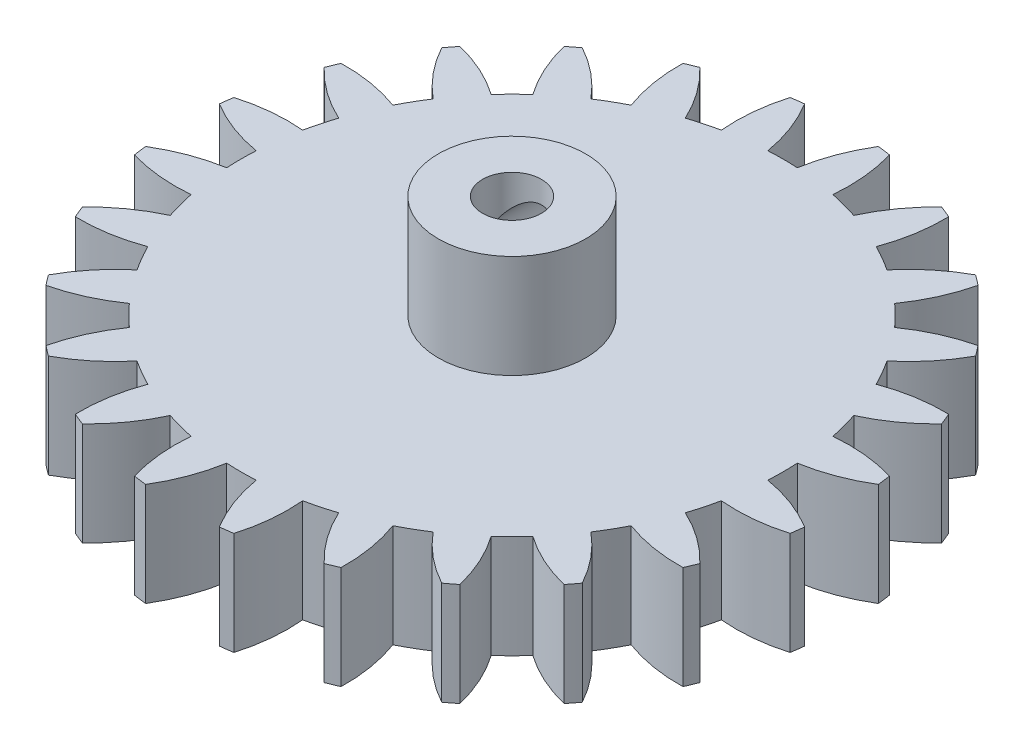
SolidWorks part; units mm, degrees
ref_plane "Front Plane" through (0, 0, 0) normal (0, 0, 1) x (1, 0, 0)
ref_plane "Top Plane" through (0, 0, 0) normal (0, 1, 0) x (1, 0, 0)
ref_plane "Right Plane" through (0, 0, 0) normal (1, 0, 0) x (0, 0, -1)
sketch "Sketch1" plane through (0, 0, 0) normal (0, 1, 0) x (1, 0, 0)
  circle A0 centre (0, 0) radius 22.5
  dimension "D1" = 45
extrude "Boss-Extrude1" add sketch "Sketch1" along normal blind 7
sketch "Sketch2" plane through (0, 7, 0) normal (0, 1, 0) x (1, 0, 0)
  line L0 (-1, 18.3607) -> (1, 18.3607) construction
  line L1 (-12.235, 16.4288) -> (12.235, 16.4288) construction
  line L2 (0, 22.3607) -> (0, 0) construction
  line L4 (2.5, 22.3607) -> (-2.5, 22.3607) construction
  arc A0 (2.5, 22.3607) -> (1, 18.3607) centre (12.235, 16.4288) ccw
  circle A1 centre (0, 0) radius 22.5 construction
  arc A2 (-2.5, 22.3607) -> (-1, 18.3607) centre (-12.235, 16.4288) cw
  arc A3 (1, 18.3607) -> (-1, 18.3607) centre (0, 0) ccw
  arc A4 (2.5, 22.3607) -> (-2.5, 22.3607) centre (0, 0) ccw
  point P8 (0, 16.4288)
  dimension "D1" = 2
  dimension "D2" = 5
  dimension "D3" = 4
  dimension "D4" = 24.47
extrude "Cut-Extrude1" cut sketch "Sketch2" against normal through all
pattern_circular "CirPattern1" count 24 every 15 about axis through (0, 0, 0) along (0, 1, 0) of "Cut-Extrude1"
sketch "Sketch3" plane through (0, 7, 0) normal (0, 1, 0) x (1, 0, 0)
  circle A0 centre (0, 0) radius 5
  dimension "D1" = 10
extrude "Boss-Extrude2" add sketch "Sketch3" along normal blind 7
sketch "Sketch4" plane through (0, 14, 0) normal (0, 1, 0) x (1, 0, 0)
  circle A0 centre (0, 0) radius 2
extrude "Cut-Extrude2" cut sketch "Sketch4" against normal through all
sketch "Sketch5" plane through (0, 0, 0) normal (0, 0, 1) x (1, 0, 0)
  line L0 (0, 14) -> (0, 10.5) construction
  line L1 (5, 14) -> (-5, 14) construction
  line L2 (2, 14) -> (-2, 14) construction
  circle A0 centre (0, 10.5) radius 2
  point P3 (0, 14)
  dimension "D1" = 3.5
extrude "Cut-Extrude3" cut sketch "Sketch5" against normal through all
